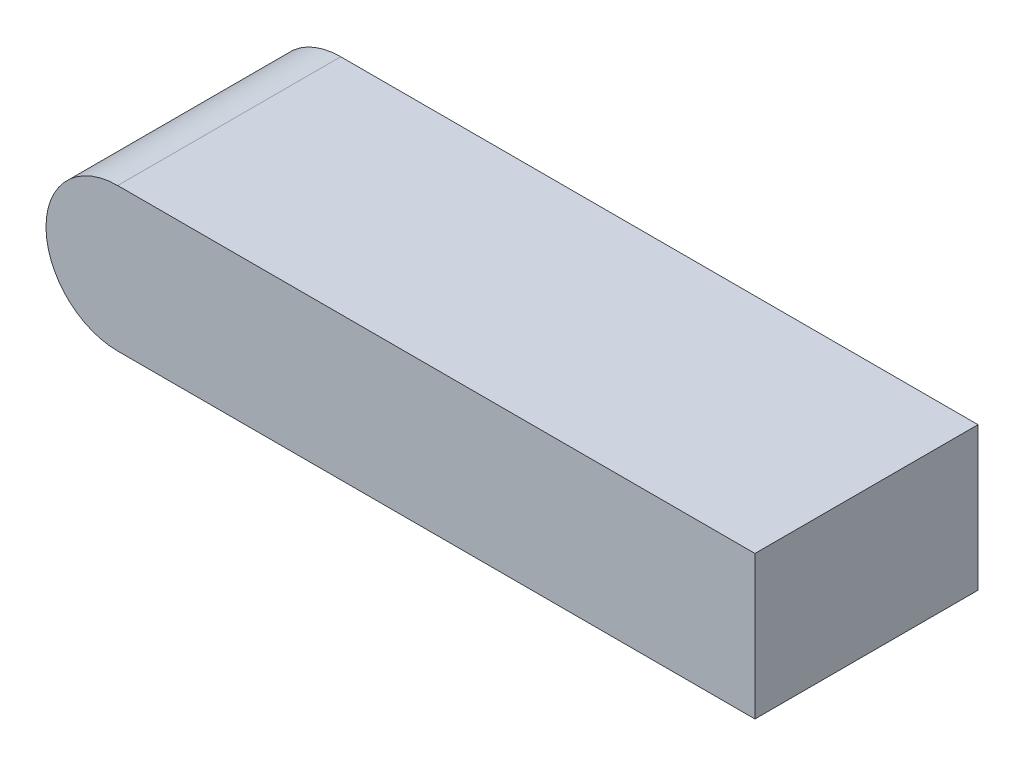
SolidWorks part; units mm, degrees
ref_plane "Front Plane" through (0, 0, 0) normal (0, 0, 1) x (1, 0, 0)
ref_plane "Top Plane" through (0, 0, 0) normal (0, 1, 0) x (1, 0, 0)
ref_plane "Right Plane" through (0, 0, 0) normal (1, 0, 0) x (0, 0, -1)
sketch "Sketch1" plane through (0, 0, 0) normal (0, 1, 0) x (1, 0, 0)
  line L1 (-63.5, -22.225) -> (63.5, -22.225)
  line L2 (-63.5, -22.225) -> (-63.5, 22.225)
  line L3 (-63.5, 22.225) -> (63.5, 22.225)
  line L4 (63.5, -22.225) -> (63.5, 22.225)
  line L5 (-63.5, -22.225) -> (63.5, 22.225) construction
  line L6 (-63.5, 22.225) -> (63.5, -22.225) construction
  point P0 (0, 0)
  dimension "D1" = 44.45
  dimension "D2" = 127
extrude "Boss-Extrude1" add sketch "Sketch1" along normal mid plane 28.575
sketch "Sketch2" plane through (0, 0, -22.225) normal (0, 0, -1) x (-1, 0, 0)
  line L0 (63.5, 14.2875) -> (63.5, -14.2875) construction
  line L1 (63.5, -14.2875) -> (63.5, 14.2875)
  arc A0 (63.5, 14.2875) -> (63.5, -14.2875) centre (63.5, 0) cw
extrude "Boss-Extrude2" add sketch "Sketch2" against normal up to surface (44.45 mm away) up to face at (0, 0, 22.225)
ref_plane "Plane1" through (-77.7875, 0, 0) normal (-1, 0, 0) x (0, 0, 1)
ref_plane "Midsection" through (-7.1438, 0, 0) normal (1, 0, 0) x (0, 0, -1)
